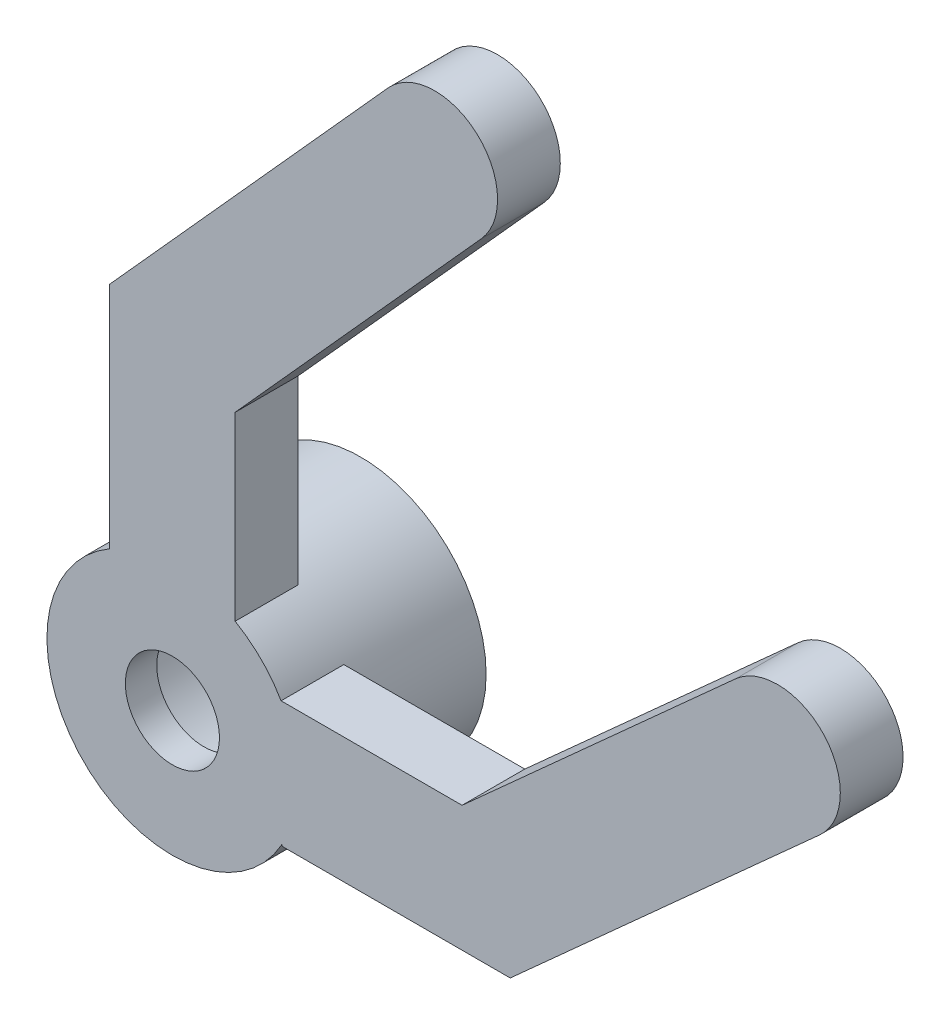
SolidWorks part; units mm, degrees
ref_plane "Plan de face" through (0, 0, 0) normal (0, 0, 1) x (1, 0, 0)
ref_plane "Plan de dessus" through (0, 0, 0) normal (0, 1, 0) x (1, 0, 0)
ref_plane "Plan de droite" through (0, 0, 0) normal (1, 0, 0) x (0, 0, -1)
sketch "Esquisse4" plane through (0, 0, 0) normal (0, 0, 1) x (1, 0, 0)
  circle A0 centre (0, 0) radius 3
  circle A1 centre (0, 0) radius 4
  dimension "D1" = 8
  dimension "D2" = 6
extrude "Boss.-Extru.1" add sketch "Esquisse4" along normal blind 6
sketch "Esquisse6" plane through (0, 0, 6) normal (0, 0, 1) x (1, 0, 0)
  circle A0 centre (0, 0) radius 1.5
  circle A1 centre (0, 0) radius 3
extrude "Boss.-Extru.2" add sketch "Esquisse6" against normal blind 1
sketch "Esquisse7" plane through (0, 0, 6) normal (0, 0, 1) x (1, 0, 0)
  line L0 (2.7525, 0) -> (10, 0)
  line L1 (0, 2.5288) -> (0, 10)
  line L2 (0, 10) -> (8.3641, 19.2893)
  line L3 (10, 0) -> (19.2893, 8.3641)
  line L4 (9.2323, 2) -> (17.951, 9.8504)
  line L5 (2, 2) -> (9.2323, 2)
  line L6 (2, 2) -> (2, 9.2323)
  line L7 (2, 9.2323) -> (9.8504, 17.951)
  line L8 (10.7677, -2) -> (20.6276, 6.8778)
  line L9 (3.5051, -2) -> (10.7677, -2)
  line L10 (-2, 3.0575) -> (-2, 10.7677)
  line L11 (-2, 10.7677) -> (6.8778, 20.6276)
  line L12 (2, 2) -> (3.5051, -2)
  line L13 (2, 2) -> (-2, 3.0575)
  line L15 (-2, -2) -> (-2, 10.7677) construction
  line L16 (-2, -2) -> (10.7677, -2) construction
  line L17 (0, 0) -> (10, 0) construction
  line L18 (0, 0) -> (0, 10) construction
  arc A0 (17.951, 9.8504) -> (20.6276, 6.8778) centre (19.2893, 8.3641) cw
  arc A1 (9.8504, 17.951) -> (6.8778, 20.6276) centre (8.3641, 19.2893) ccw
  dimension "D1" = 10
  dimension "D2" = 10
  dimension "D3" = 12.5
  dimension "D4" = 138
  dimension "D5" = 12.5
  dimension "D6" = 138
  dimension "D7" = 2
  dimension "D8" = 2
extrude "Boss.-Extru.3" add sketch "Esquisse7" against normal blind 2
